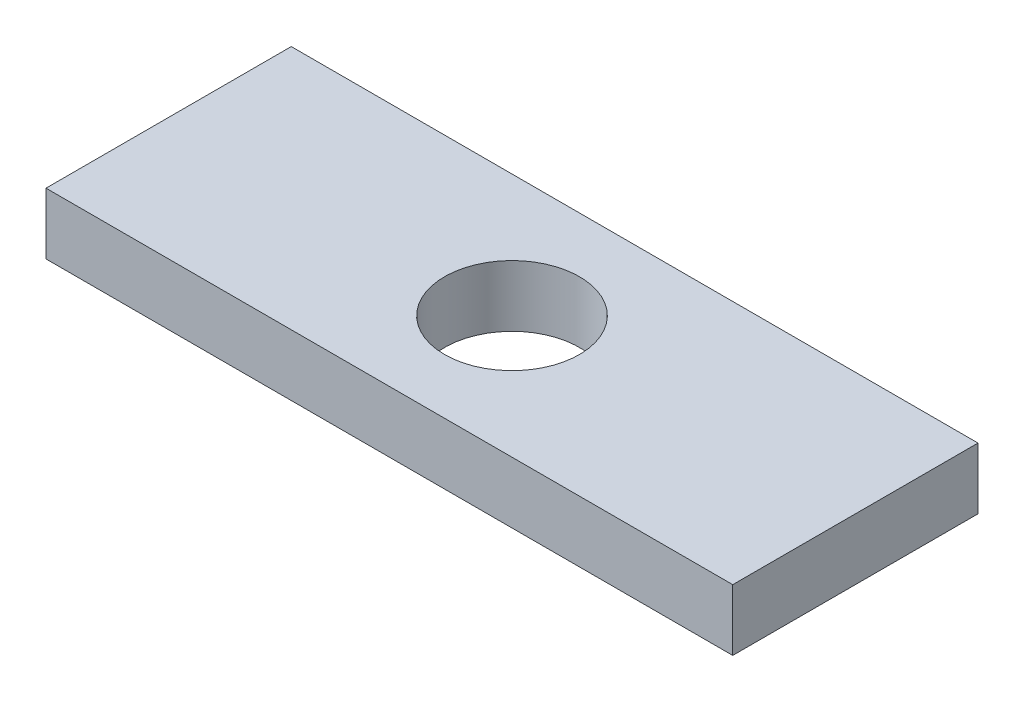
SolidWorks part; units mm, degrees
ref_plane "Front Plane" through (0, 0, 0) normal (0, 0, 1) x (1, 0, 0)
ref_plane "Top Plane" through (0, 0, 0) normal (0, 1, 0) x (1, 0, 0)
ref_plane "Right Plane" through (0, 0, 0) normal (1, 0, 0) x (0, 0, -1)
sketch "Sketch1" plane through (0, 0, 0) normal (0, 1, 0) x (1, 0, 0)
  line L1 (-17.78, 6.35) -> (17.78, 6.35)
  line L2 (-17.78, 6.35) -> (-17.78, -6.35)
  line L3 (-17.78, -6.35) -> (17.78, -6.35)
  line L4 (17.78, 6.35) -> (17.78, -6.35)
  circle A0 centre (0, 0) radius 3.4925
  point P4 (0, 6.35)
  point P5 (17.78, 0)
  dimension "D3" = 6.985
  dimension "D1" = 35.56
  dimension "D2" = 12.7
extrude "Boss-Extrude1" add sketch "Sketch1" along normal blind 3.175 contours L3 L4 L1 L2 | A0
